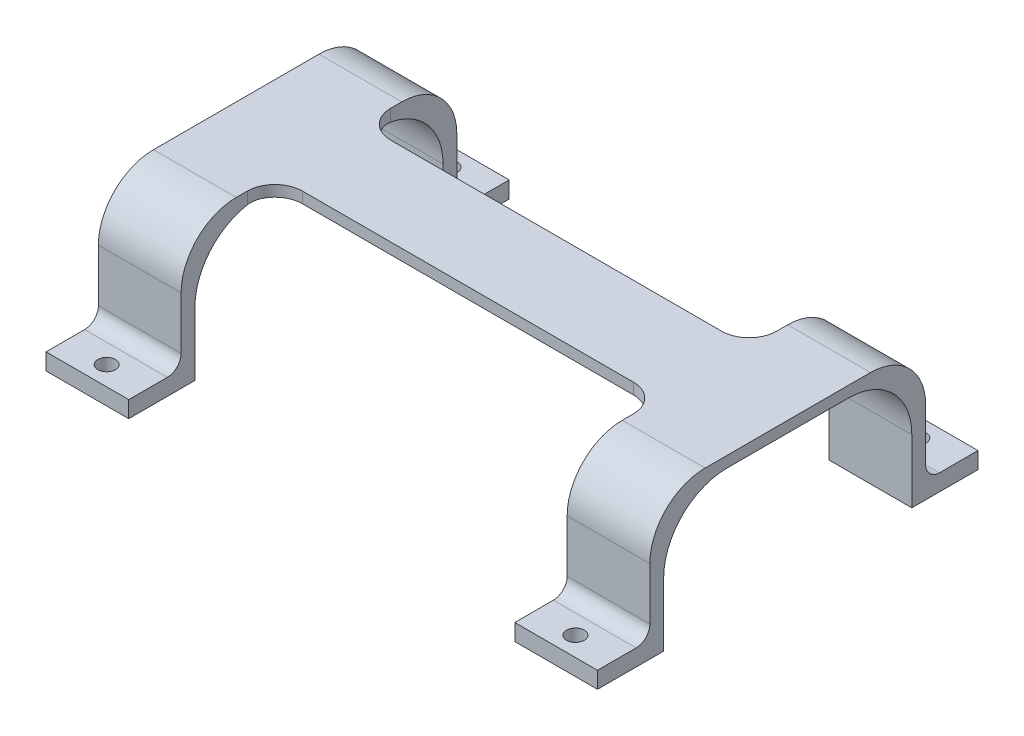
SolidWorks part; units mm, degrees
ref_plane "Front Plane" through (0, 0, 0) normal (0, 0, 1) x (1, 0, 0)
ref_plane "Top Plane" through (0, 0, 0) normal (0, 1, 0) x (1, 0, 0)
ref_plane "Right Plane" through (0, 0, 0) normal (1, 0, 0) x (0, 0, -1)
sketch "Sketch1" plane through (0, 0, 0) normal (1, 0, 0) x (0, 0, -1)
  line L0 (0, 0) -> (0, 20875.6439) construction
  line L1 (0, 0) -> (20875.6439, 0) construction
  line L2 (-11, 11.5) -> (11, 11.5)
  line L4 (-22.5, 0) -> (-22.5, -11.5)
  line L5 (-22.5, -11.5) -> (-34.5, -11.5)
  line L6 (-34.5, -11.5) -> (-34.5, -8.5)
  line L7 (-34.5, -8.5) -> (-25, -8.5)
  line L8 (-25, -8.5) -> (-25, 0)
  line L9 (-25, 0) -> (-25, 3.5)
  line L10 (-15, 13.5) -> (15, 13.5)
  line L11 (25, 0) -> (25, 3.5)
  line L12 (22.5, 0) -> (22.5, -11.5)
  line L13 (25, -8.5) -> (25, 0)
  line L14 (34.5, -8.5) -> (25, -8.5)
  line L15 (34.5, -11.5) -> (34.5, -8.5)
  line L16 (22.5, -11.5) -> (34.5, -11.5)
  arc A0 (-11, 11.5) -> (-22.5, 0) centre (-11, 0) ccw
  arc A1 (11, 11.5) -> (22.5, 0) centre (11, 0) cw
  arc A2 (-15, 13.5) -> (-25, 3.5) centre (-15, 3.5) ccw
  arc A3 (15, 13.5) -> (25, 3.5) centre (15, 3.5) cw
  point P10 (0, 11.5)
  point P13 (0, -8.4966)
  point P20 (25, 1.75)
  point P22 (-25, 1.75)
  point P24 (0, 13.5)
  dimension "D7" = 10
  dimension "D1" = 45
  dimension "D2" = 11.5
  dimension "D3" = 23
  dimension "D4" = 3
  dimension "D5" = 2.5
  dimension "D6" = 2
  dimension "D8" = 12
extrude "Boss-Extrude1" add sketch "Sketch1" along normal mid plane 100
sketch "Sketch2" plane through (0, 13.5, 0) normal (0, 1, 0) x (1, 0, 0)
  line L0 (0, 0) -> (50000, 0) construction
  line L1 (0, 0) -> (0, 50000) construction
  line L2 (35, 34.5) -> (-35, 34.5)
  line L3 (50, 34.5) -> (-50, 34.5) construction
  line L4 (-35, 34.5) -> (-35, 8)
  line L5 (-35, 8) -> (35, 8)
  line L7 (-50, 34.5) -> (-50, 25) construction
  line L8 (35, 34.5) -> (35, 8)
  line L9 (35, -34.5) -> (35, -8)
  line L10 (-35, -8) -> (35, -8)
  line L11 (-35, -34.5) -> (-35, -8)
  line L12 (35, -34.5) -> (-35, -34.5)
  point P13 (-50, 29.75)
  point P15 (0, 8)
  point P16 (0, 34.5)
  point P20 (0, -34.5)
  point P21 (0, -8)
  dimension "D1" = 15
  dimension "D2" = 8
extrude "Cut-Extrude1" cut sketch "Sketch2" against normal through all both and the other way through all
fillet "Fillet1" radius 2.5 2 edges at (42.5, -8.5, -25) (42.5, -8.5, 25)
fillet "Fillet2" radius 5 4 edges at (35, 12.5, -8) (35, 12.5, 8) (-35, 12.5, 8) (-35, 12.5, -8)
sketch "Sketch3" plane through (0, -8.5, 0) normal (0, 1, 0) x (1, 0, 0)
  line L0 (0, 0) -> (0, -50000) construction
  line L1 (0, 0) -> (-50000, 0) construction
  line L2 (42.5, -34.5) -> (42.5, -27.5) construction
  line L3 (50, -34.5) -> (35, -34.5) construction
  line L4 (50, -27.5) -> (35, -27.5) construction
  line L5 (35, -31) -> (50, -31) construction
  line L6 (35, -27.5) -> (35, -34.5) construction
  line L7 (50, -27.5) -> (50, -34.5) construction
  line L8 (-35, -31) -> (-50, -31) construction
  line L9 (-42.5, -34.5) -> (-42.5, -27.5) construction
  circle A0 centre (42.5, -31) radius 1.6
  circle A1 centre (42.5, 31) radius 1.6
  circle A2 centre (-42.5, 31) radius 1.6
  circle A3 centre (-42.5, -31) radius 1.6
  dimension "D1" = 3.2
extrude "Cut-Extrude2" cut sketch "Sketch3" against normal through all and the other way through all
